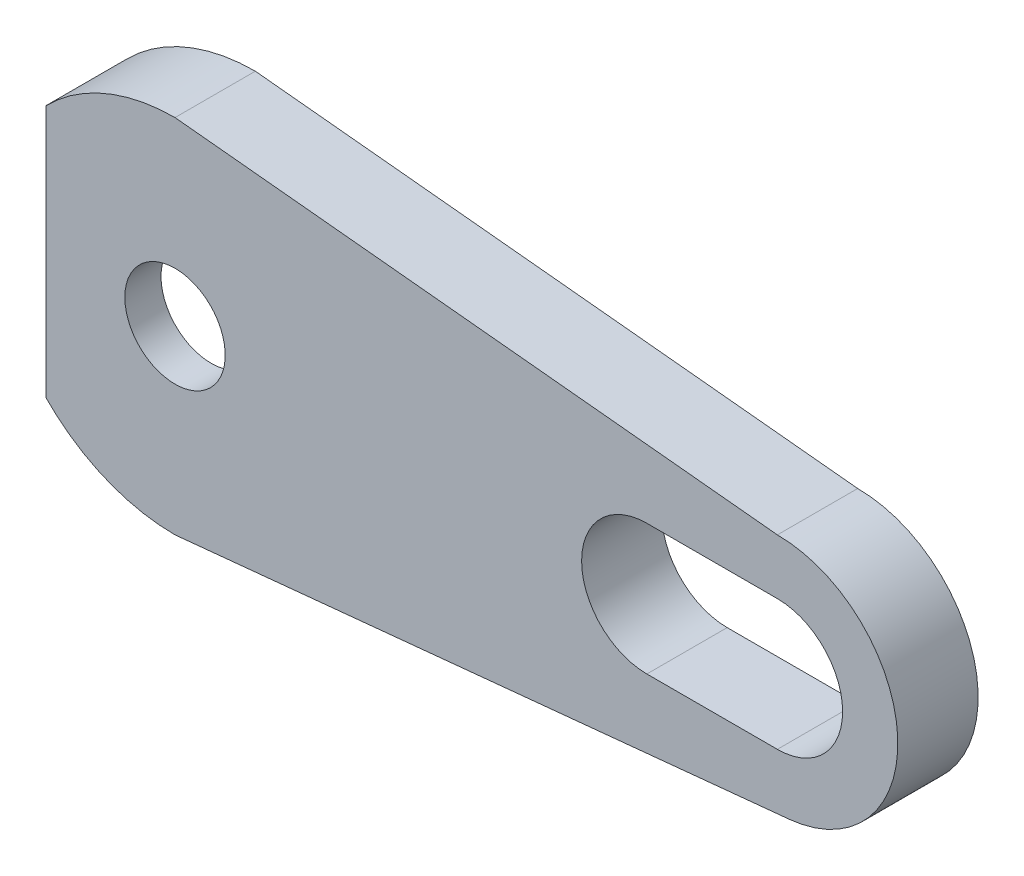
SolidWorks part; units mm, degrees
ref_plane "Front Plane" through (0, 0, 0) normal (0, 0, 1) x (1, 0, 0)
ref_plane "Top Plane" through (0, 0, 0) normal (0, 1, 0) x (1, 0, 0)
ref_plane "Right Plane" through (0, 0, 0) normal (1, 0, 0) x (0, 0, -1)
sketch "Esquisse1" plane through (0, 0, 0) normal (0, 0, 1) x (1, 0, 0)
  line L0 (-4.3758, 4.25) -> (-6.4265, 6.3008)
  line L1 (4.3758, 4.25) -> (17.3156, 2.7822)
  line L2 (17.3156, -2.7822) -> (4.3758, -4.25)
  line L3 (23.5, 3.25) -> (30, 3.25)
  line L4 (0, 9) -> (30, 6)
  line L5 (0, -9) -> (30.5912, -5.9708)
  line L6 (-4.3758, -4.25) -> (-6.4265, -6.3008)
  line L7 (23.5, -3.25) -> (30, -3.25)
  arc A0 (4.3758, 4.25) -> (-4.3758, 4.25) centre (0, 0) ccw
  arc A1 (17.3156, -2.7822) -> (17.3156, 2.7822) centre (17, 0) ccw
  arc A2 (4.3758, -4.25) -> (-4.3758, -4.25) centre (0, 0) cw
  arc A3 (-6.4265, 6.3008) -> (0, 9) centre (0, 0) cw
  arc A4 (30, 3.25) -> (30, -3.25) centre (30, 0) cw
  arc A5 (-6.4265, -6.3008) -> (0, -9) centre (0, 0) ccw
  arc A6 (30, 6) -> (30.5912, -5.9708) centre (30, 0) cw
  arc A7 (23.5, 3.25) -> (23.5, -3.25) centre (23.5, 0) ccw
  dimension "D2" = 6.1
  dimension "D3" = 2.8
  dimension "D5" = 3.25
  dimension "D6" = 9
  dimension "D8" = 30
  dimension "D1" = 8.5
  dimension "D4" = 17
  dimension "D7" = 23.5
  dimension "D9" = 6
  dimension "D10" = 6.5
extrude "Main" add sketch "Esquisse1" along normal blind 4
sketch "Esquisse2" plane through (0, 0, 4) normal (0, 0, -1) x (-1, 0, 0)
  line L0 (0, -9) -> (-13.3031, -7.6827)
  line L1 (0, -9) -> (-30.5912, -5.9708) construction
  line L2 (0, -9) -> (-30.5912, -5.9708) construction
  line L3 (0, 9) -> (-13.3031, 7.6697)
  line L4 (6.4265, -6.3008) -> (6.4265, 6.3008)
  line L5 (-30, 6) -> (0, 9) construction
  line L6 (-30, 6) -> (0, 9) construction
  line L7 (0, -9) -> (-30.5912, -5.9708) construction
  line L10 (6.4265, 6.3008) -> (4.3758, 4.25) construction
  arc A0 (6.4265, 6.3008) -> (0, 9) centre (0, 0) ccw construction
  arc A1 (0, -9) -> (6.4265, -6.3008) centre (0, 0) ccw
  circle A2 centre (0, 0) radius 2.5
  arc A3 (6.4265, 6.3008) -> (0, 9) centre (0, 0) ccw
  arc A4 (-13.3031, -7.6827) -> (-13.3031, 7.6697) centre (-12.5355, -0.0065) cw
  arc A5 (-23.5, -3.25) -> (-23.5, 3.25) centre (-23.5, 0) ccw construction
  arc A6 (0, -9) -> (6.4265, -6.3008) centre (0, 0) ccw construction
  dimension "D1" = 5
extrude "Boss-Extrude1" add sketch "Esquisse2" along normal blind 1.8
